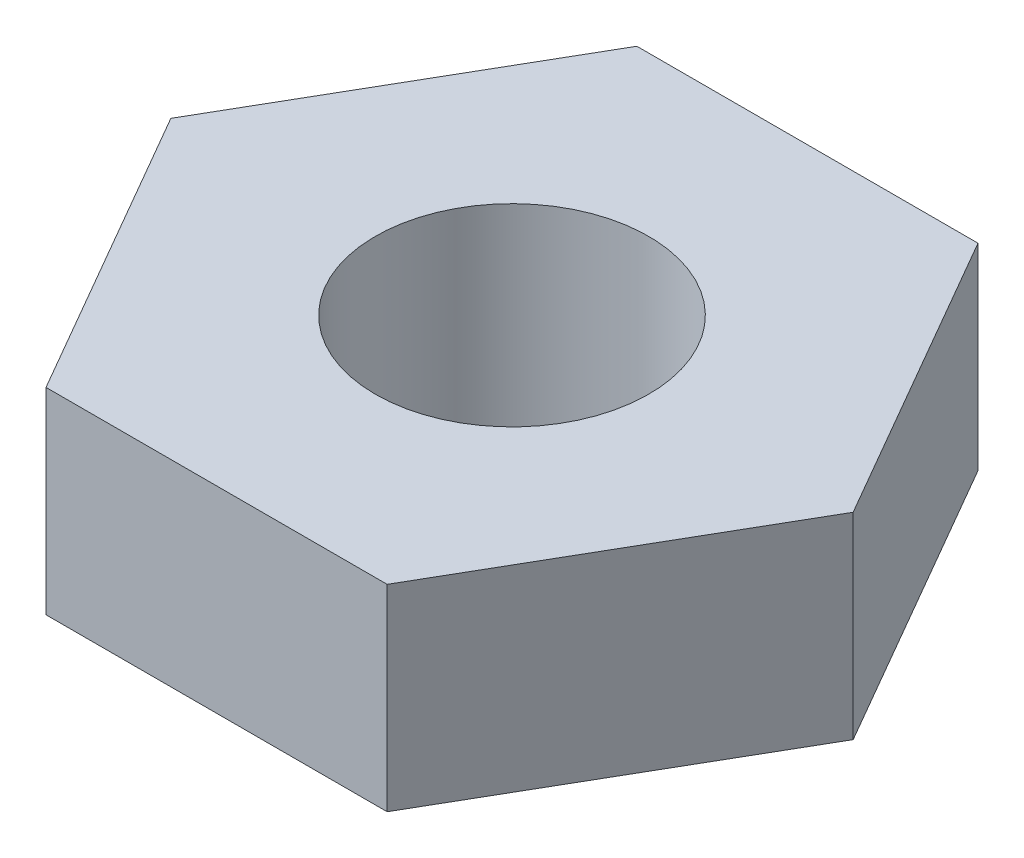
SolidWorks part; units mm, degrees
ref_plane "Front Plane" through (0, 0, 0) normal (0, 0, 1) x (1, 0, 0)
ref_plane "Top Plane" through (0, 0, 0) normal (0, 1, 0) x (1, 0, 0)
ref_plane "Right Plane" through (0, 0, 0) normal (1, 0, 0) x (0, 0, -1)
sketch "Sketch1" plane through (0, 0, 0) normal (0, 1, 0) x (1, 0, 0)
  line L1 (5.1962, 0) -> (2.5981, 4.5)
  line L2 (2.5981, 4.5) -> (-2.5981, 4.5)
  line L3 (-2.5981, 4.5) -> (-5.1962, 0)
  line L4 (-5.1962, 0) -> (-2.5981, -4.5)
  line L5 (-2.5981, -4.5) -> (2.5981, -4.5)
  line L6 (2.5981, -4.5) -> (5.1962, 0)
  circle A0 centre (0, 0) radius 4.5 construction
  circle A1 centre (0, 0) radius 2.0828
  point P10 (-3.3899, 3.9381)
  point P11 (0, 0)
  dimension "D2" = 4.1656
  dimension "D1" = 9
extrude "Boss-Extrude1" add sketch "Sketch1" along normal blind 3
